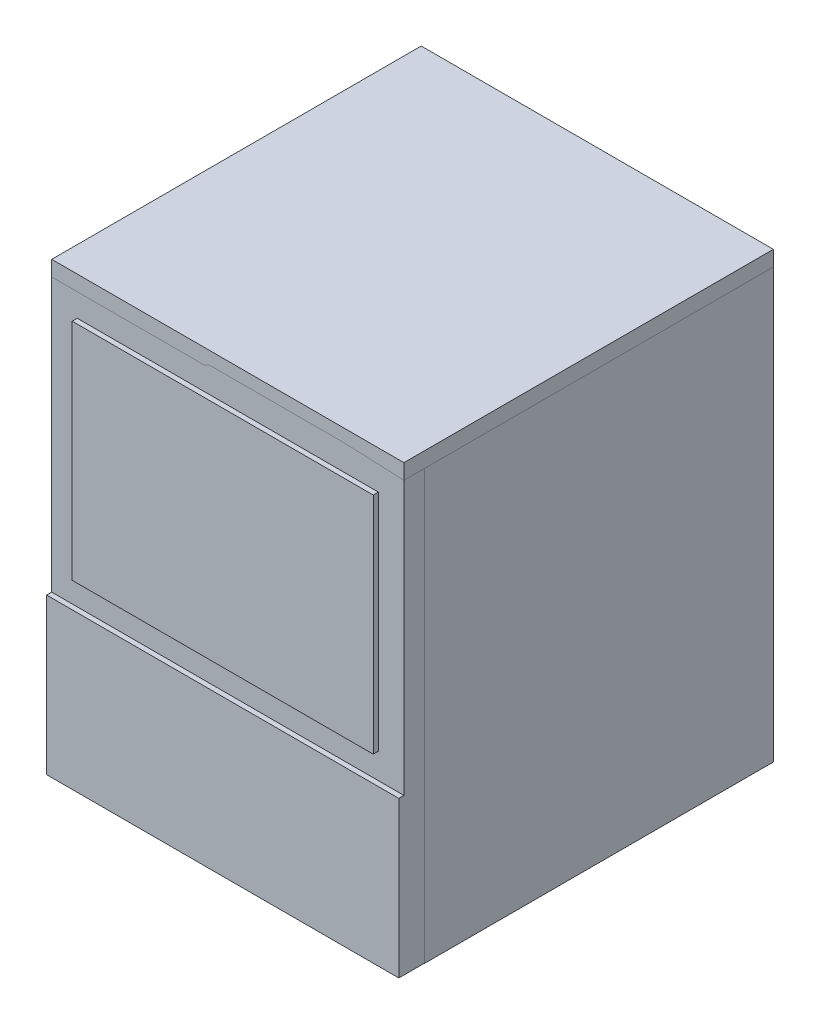
SolidWorks part; units mm, degrees
ref_plane "Front Plane" through (0, 0, 0) normal (0, 0, 1) x (1, 0, 0)
ref_plane "Top Plane" through (0, 0, 0) normal (0, 1, 0) x (1, 0, 0)
ref_plane "Right Plane" through (0, 0, 0) normal (1, 0, 0) x (0, 0, -1)
ref_plane "Plane1" through (0, -89, 0) normal (0, 1, 0) x (1, 0, 0)
sketch "Sketch2" plane through (0, -89, 0) normal (0, 1, 0) x (1, 0, 0)
  line L1 (-345, 341.95) -> (345, 341.95)
  line L2 (-345, 341.95) -> (-345, -341.95)
  line L3 (-345, -341.95) -> (345, -341.95)
  line L4 (345, 341.95) -> (345, -341.95)
  line L5 (0, -341.95) -> (0, 341.95) construction
  line L6 (-345, 0) -> (345, 0) construction
  point P0 (0, 0)
  dimension "D1" = 683.9
  dimension "D2" = 690
extrude "Boss-Extrude1" add sketch "Sketch2" along normal blind 0.5
sketch "Sketch4" plane through (0, -89, 0) normal (0, 1, 0) x (1, 0, 0)
  line L0 (-345, 341.95) -> (345, 341.95)
  line L1 (345, 341.95) -> (345, -341.95)
  line L2 (345, 341.95) -> (345, -341.95) construction
  line L3 (345, -341.95) -> (-345, -341.95)
  line L4 (-345, 341.95) -> (-345, -341.95) construction
  line L5 (-345, -341.95) -> (-345, 341.95)
  line L6 (0, 341.95) -> (0, 331.95) construction
  line L7 (0, -341.95) -> (0, 341.95) construction
  line L8 (345, 0) -> (335, 0) construction
  line L9 (-345, 0) -> (345, 0) construction
  line L10 (0, -341.95) -> (0, -331.95) construction
  line L11 (-345, 0) -> (-335, 0) construction
  line L17 (-335, 331.95) -> (335, 331.95)
  line L18 (-335, 331.95) -> (-335, -331.95)
  line L19 (-335, -331.95) -> (335, -331.95)
  line L20 (335, 331.95) -> (335, -331.95)
  dimension "D1" = 663.9
  dimension "D2" = 670
  dimension "D3" = 10
  dimension "D4" = 10
  dimension "D5" = 683.9
  dimension "D6" = 10
extrude "Boss-Extrude3" add sketch "Sketch4" along normal blind 845 separate body
ref_plane "Plane2" through (0, 781, 0) normal (0, 1, 0) x (1, 0, 0)
sketch "Sketch12" plane through (0, 781, 0) normal (0, 1, 0) x (1, 0, 0)
  line L1 (-345, 341.95) -> (345, 341.95)
  line L2 (-345, 341.95) -> (-345, -381.95)
  line L3 (-345, -381.95) -> (345, -381.95)
  line L4 (345, 341.95) -> (345, -381.95)
  dimension "D1" = 723.9
  dimension "D2" = 690
extrude "Boss-Extrude4" add sketch "Sketch12" against normal blind 10 separate body
ref_plane "Plane3" through (0, 0, 341.95) normal (0, 0, 1) x (1, 0, 0)
sketch "Sketch13" plane through (0, 781, 0) normal (0, 1, 0) x (1, 0, 0)
  line L0 (-335, -371.95) -> (-335, 331.95)
  line L1 (-345, -381.95) -> (345, -381.95)
  line L2 (-345, -381.95) -> (-345, 341.95)
  line L3 (-345, 341.95) -> (345, 341.95)
  line L4 (345, -381.95) -> (345, 341.95)
  line L5 (-335, 331.95) -> (335, 331.95)
  line L6 (335, -371.95) -> (335, 331.95)
  line L7 (-335, -371.95) -> (335, -371.95)
  dimension "D1" = 723.9
  dimension "D2" = 690
  dimension "D3" = 10
extrude "Boss-Extrude5" add sketch "Sketch13" against normal blind 30
sketch "Sketch11" plane through (0, 0, 341.95) normal (0, 0, 1) x (1, 0, 0)
  line L0 (0, 756) -> (0, 656) construction
  line L1 (-345, 756) -> (345, 756) construction
  line L2 (0, -88.5) -> (0, 306.3) construction
  line L3 (-345, -88.5) -> (345, -88.5) construction
  line L4 (-345, 333.5) -> (-265, 333.5) construction
  line L5 (-345, 756) -> (-345, -89) construction
  line L6 (345, 333.5) -> (265, 333.5) construction
  line L7 (345, 756) -> (345, -89) construction
  line L17 (-265, 656) -> (265, 656)
  line L18 (-265, 656) -> (-265, 306.3)
  line L19 (-265, 306.3) -> (265, 306.3)
  line L20 (265, 656) -> (265, 306.3)
  dimension "D1" = 80
  dimension "D2" = 80
  dimension "D3" = 394.8
  dimension "D4" = 100
  dimension "D5" = 349.7
  dimension "D6" = 530
extrude "Cut-Extrude1" cut sketch "Sketch11" against normal blind 10
ref_plane "Plane4" through (0, 0, 381.95) normal (0, 0, 1) x (1, 0, 0)
sketch "Sketch14" plane through (0, 0, 381.95) normal (0, 0, 1) x (1, 0, 0)
  line L0 (0, 756) -> (0, 746) construction
  line L1 (-345, 756) -> (345, 756) construction
  line L2 (0, 746) -> (0, 716) construction
  line L3 (-345, 333.5) -> (-305, 333.5) construction
  line L4 (-345, 756) -> (-345, -89) construction
  line L5 (345, 333.5) -> (305, 333.5) construction
  line L6 (345, 756) -> (345, -89) construction
  line L7 (0, 216.3) -> (0, 226.3) construction
  line L8 (-345, -88.5) -> (345, -88.5)
  line L9 (-345, -88.5) -> (-345, 216.3)
  line L10 (-345, 216.3) -> (345, 216.3)
  line L11 (345, -88.5) -> (345, 216.3)
  line L12 (-305, 333.5) -> (-295, 333.5) construction
  line L13 (305, 333.5) -> (295, 333.5) construction
  line L15 (0, 226.3) -> (0, 256.3) construction
  line L16 (0, 256.3) -> (0, 266.3) construction
  line L23 (0, 716) -> (0, 706) construction
  line L25 (-295, 706) -> (295, 706)
  line L26 (-295, 706) -> (-295, 266.3)
  line L27 (-295, 266.3) -> (295, 266.3)
  line L28 (295, 706) -> (295, 266.3)
  dimension "D1" = 304.8
  dimension "D2" = 690
  dimension "D3" = 40
  dimension "D4" = 10
  dimension "D5" = 10
  dimension "D6" = 40
  dimension "D7" = 10
  dimension "D8" = 30
  dimension "D9" = 10
  dimension "D10" = 10
  dimension "D11" = 439.7
  dimension "D12" = 590
sketch "Sketch15" plane through (0, 0, 381.95) normal (0, 0, 1) x (1, 0, 0)
  line L1 (-345, 756) -> (345, 756)
  line L2 (-345, 756) -> (-345, -88.5)
  line L3 (-345, -88.5) -> (345, -88.5)
  line L4 (345, 756) -> (345, -88.5)
  dimension "D1" = 844.5
  dimension "D2" = 690
extrude "Boss-Extrude6" add sketch "Sketch15" against normal blind 10 separate body
extrude "Boss-Extrude7" add sketch "Sketch14" against normal blind 30 and the other way blind 10
sketch "Sketch17" plane through (0, 0, 381.95) normal (0, 0, 1) x (1, 0, 0)
  line L0 (335, 746) -> (335, -78.5)
  line L1 (345, 756) -> (-345, 756)
  line L2 (345, 756) -> (345, -88.5)
  line L3 (345, -88.5) -> (-345, -88.5)
  line L4 (-345, 756) -> (-345, -88.5)
  line L5 (335, -78.5) -> (-335, -78.5)
  line L6 (-335, 746) -> (-335, -78.5)
  line L7 (335, 746) -> (-335, 746)
  dimension "D1" = 844.5
  dimension "D2" = 690
  dimension "D3" = 10
extrude "Boss-Extrude8" add sketch "Sketch17" against normal blind 40
